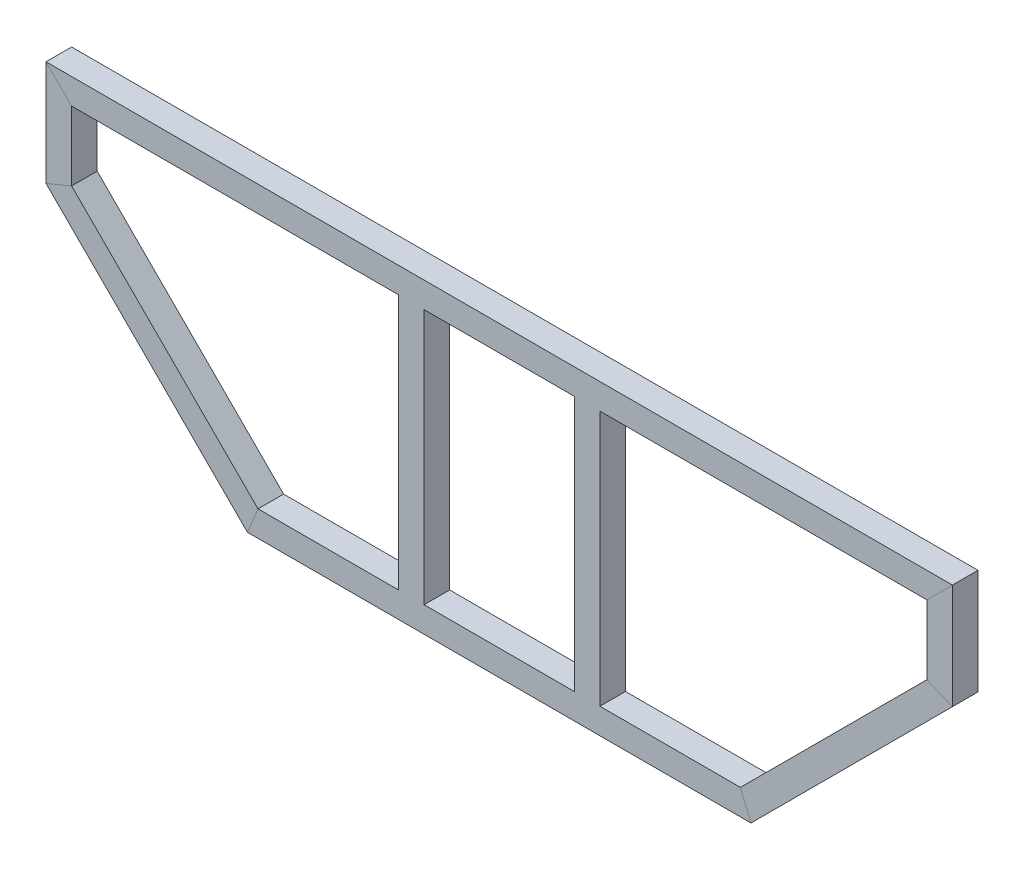
SolidWorks part; units mm, degrees
material "Ductile Iron (SN)"
ref_plane "Front Plane" through (0, 0, 0) normal (0, 0, 1) x (1, 0, 0)
ref_plane "Top Plane" through (0, 0, 0) normal (0, 1, 0) x (1, 0, 0)
ref_plane "Right Plane" through (0, 0, 0) normal (1, 0, 0) x (0, 0, -1)
sketch "Sketch3" plane through (0, 0, 0) normal (0, 0, 1) x (1, 0, 0)
  line L0 (-250, -304.6) -> (250, -304.6)
  line L1 (-250, -304.6) -> (-450, -104.6)
  line L2 (250, -304.6) -> (450, -104.6)
  line L4 (-450, 0) -> (-450, -104.6)
  line L5 (450, 0) -> (450, -104.6)
  line L6 (-450, 0) -> (450, 0)
  point P3 (0, -304.6)
  point P8 (0, 0)
  point P13 (0, 0)
  point P15 (0, 0)
  point P16 (0, 0)
  point P17 (450, 0)
  point P18 (0, 0)
  point P21 (0, 0)
  dimension "D1" = 304.6
  dimension "D2" = 135
  dimension "D3" = 500
  dimension "D4" = 900
sketch "Sketch4" plane through (0, 0, 0) normal (1, 0, 0) x (0, 0, -1)
  line L0 (1.2, -280.4) -> (24.2, -280.4)
  line L1 (0, -304.6) -> (25.4, -304.6)
  line L2 (0, -304.6) -> (0, -279.2)
  line L3 (0, -279.2) -> (25.4, -279.2)
  line L4 (25.4, -304.6) -> (25.4, -279.2)
  line L5 (24.2, -303.4) -> (24.2, -280.4)
  line L6 (1.2, -303.4) -> (24.2, -303.4)
  line L7 (1.2, -303.4) -> (1.2, -280.4)
  point P4 (0, 0)
  dimension "D1" = 25.4
  dimension "D2" = 1.2
sweep "Sweep1" add profiles "Sketch4" path "Sketch3"
sketch "Sketch5" plane through (-272.713, -279.2, 0) normal (0, 1, 0) x (-1, 0, 0)
  line L0 (-22.713, 0) -> (177.287, 0) construction
  line L1 (-372.713, -25.4) -> (-347.313, -25.4)
  line L2 (-372.713, -25.4) -> (-372.713, 0)
  line L3 (-372.713, 0) -> (-347.313, 0)
  line L4 (-347.313, -25.4) -> (-347.313, 0)
  line L5 (-348.513, -24.2) -> (-348.513, -1.2)
  line L6 (-172.713, -25.4) -> (-198.113, -25.4)
  line L7 (-172.713, -25.4) -> (-172.713, 0)
  line L8 (-172.713, 0) -> (-198.113, 0)
  line L9 (-198.113, -25.4) -> (-198.113, 0)
  line L10 (-371.513, -1.2) -> (-348.513, -1.2)
  line L11 (-371.513, -24.2) -> (-371.513, -1.2)
  line L12 (-371.513, -24.2) -> (-348.513, -24.2)
  line L13 (-196.913, -24.2) -> (-196.913, -1.2)
  line L14 (-173.913, -1.2) -> (-196.913, -1.2)
  line L15 (-173.913, -24.2) -> (-173.913, -1.2)
  line L16 (-173.913, -24.2) -> (-196.913, -24.2)
  line L17 (-272.713, 35.388) -> (-272.713, -374.0224) construction
  dimension "D2" = 200
  dimension "D4" = 25.4
  dimension "D3" = 100
  dimension "D1" = 1.2
extrude "Boss-Extrude2" add sketch "Sketch5" along normal up to surface (253.8 mm away) up to face at (0, -25.4, -12.7)
equation "\"pipeWidth\"=2.54"
equation "\"pipeThickness\"=0.12"
equation "\"D1@Sketch4\"= \"pipeWidth\""
equation "\"D4@Sketch5\"=\"pipeWidth\""
